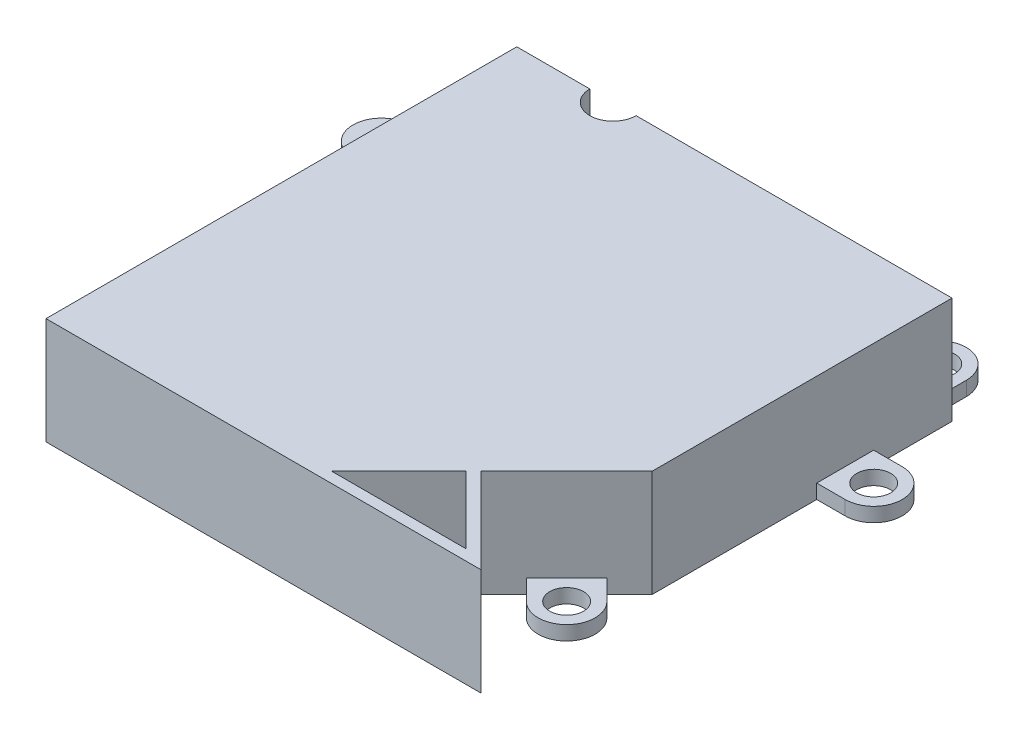
SolidWorks part; units mm, degrees
ref_plane "Front Plane" through (0, 0, 0) normal (0, 0, 1) x (1, 0, 0)
ref_plane "Top Plane" through (0, 0, 0) normal (0, 1, 0) x (1, 0, 0)
ref_plane "Right Plane" through (0, 0, 0) normal (1, 0, 0) x (0, 0, -1)
sketch "Sketch2" plane through (0, 0, 0) normal (0, 1, 0) x (1, 0, 0)
  line L0 (0, 0) -> (0, 66.1126)
  line L1 (0, 66.1126) -> (64.116, 66.1126)
  line L2 (64.116, 66.1126) -> (64.116, 23.9916)
  line L3 (64.116, 23.9916) -> (40.1244, 0)
  line L4 (40.1244, 0) -> (0, 0)
  line L5 (52.1202, 11.9958) -> (64.116, 0)
  line L6 (64.116, 0) -> (40.1244, 0)
  line L7 (52.1202, 11.9958) -> (51.0595, 10.9351)
  line L8 (51.0595, 10.9351) -> (60.4947, 1.5)
  line L9 (60.4947, 1.5) -> (41.6244, 1.5)
  dimension "D1" = 64.116
  dimension "D2" = 42.121
  dimension "D3" = 66.1126
  dimension "D4" = 135
  dimension "D5" = 40.1244
  dimension "D6" = 1.5
  dimension "D7" = 1.5
extrude "Boss-Extrude2" add sketch "Sketch2" along normal blind 15 contours L4 L3 L2 L1 L0 | L8 L9 L3 L6 L5
sketch "Sketch3" plane through (0, 0, 0) normal (0, -1, 0) x (1, 0, 0)
  line L0 (64.116, -66.1126) -> (62.616, -66.1126)
  line L1 (0, -66.1126) -> (64.116, -66.1126) construction
  line L2 (62.616, -66.1126) -> (62.616, -24.6129)
  line L3 (62.616, -24.6129) -> (39.5031, -1.5)
  line L4 (39.5031, -1.5) -> (1.5, -1.5)
  line L5 (1.5, -1.5) -> (1.5, -64.6126)
  line L6 (1.5, -64.6126) -> (62.616, -64.6126)
  line L7 (0, 0) -> (0, -66.1126) construction
  line L8 (64.116, 0) -> (0, 0) construction
  line L9 (64.116, -23.9916) -> (52.1202, -11.9958) construction
  line L10 (64.116, -66.1126) -> (64.116, -23.9916) construction
  dimension "D1" = 1.5
  dimension "D2" = 1.5
  dimension "D3" = 1.5
  dimension "D4" = 1.5
  dimension "D5" = 1.5
extrude "Cut-Extrude1" cut sketch "Sketch3" against normal blind 13.5 contours L5 L6 L2 L3 L4
sketch "Sketch4" plane through (0, 0, 0) normal (0, -1, 0) x (1, 0, 0)
  line L0 (62.616, -64.6126) -> (41.616, -64.6126)
  line L1 (1.5, -64.6126) -> (62.616, -64.6126) construction
  line L2 (41.616, -64.6126) -> (19.616, -64.6126)
  line L3 (41.616, -64.6126) -> (41.616, -66.1126)
  line L4 (0, -66.1126) -> (64.116, -66.1126) construction
  line L5 (41.616, -66.1126) -> (19.616, -66.1126)
  line L6 (19.616, -66.1126) -> (19.616, -64.6126)
  line M3 (62.616, -64.6126) -> (1.5, -64.6126)
  line M13 (0, -66.1126) -> (64.116, -66.1126)
  dimension "D1" = 21
  dimension "D2" = 22
extrude "Cut-Extrude2" cut sketch "Sketch4" against normal blind 7.5 contours L6 L3 M13 M3
sketch "Sketch5" plane through (0, 0, 0) normal (0, -1, 0) x (1, 0, 0)
  line L0 (64.116, -66.1126) -> (56.8197, -66.1126)
  line L2 (41.616, -66.1126) -> (64.116, -66.1126) construction
  line L3 (56.8197, -66.1126) -> (56.8197, -64.6126)
  line L4 (41.616, -64.6126) -> (62.616, -64.6126) construction
  line L5 (56.8197, -66.1126) -> (56.8197, -65.3626)
  line L6 (56.8197, -65.3626) -> (64.116, -65.3626)
  line L7 (64.116, -66.1126) -> (64.116, -23.9916) construction
  line L8 (56.8197, -66.1126) -> (56.8197, -66.0126)
  dimension "D1" = 0.1
sketch "Sketch6" plane through (0, 15, 0) normal (0, 1, 0) x (1, 0, 0)
  line L0 (64.116, 66.1126) -> (64.116, 65.3626)
  line L1 (64.116, 66.1126) -> (64.116, 23.9916) construction
  dimension "D1" = 0.75
ref_plane "Plane1" through (0, 0, -65.3626) normal (0, 0, 1) x (1, 0, 0)
sketch "Sketch16" plane through (0, 0, -66.1126) normal (0, 0, -1) x (-1, 0, 0)
  line L0 (-19.616, 0) -> (-9.616, 0)
  line L1 (0, 0) -> (-19.616, 0) construction
  line L2 (-9.616, 0) -> (-9.616, 9.5)
  line L3 (-9.616, 9.5) -> (-54.116, 9.5)
  line L4 (-54.116, 9.5) -> (-54.116, 0)
  line L5 (-41.616, 0) -> (-64.116, 0) construction
  line L6 (-54.116, 0) -> (-41.616, 0)
  line L7 (-41.616, 0) -> (-41.616, 7.5)
  line L8 (-41.616, 7.5) -> (-19.616, 7.5)
  line L9 (-19.616, 7.5) -> (-19.616, 0)
  dimension "D1" = 10
  dimension "D2" = 2
  dimension "D3" = 12.5
extrude "Cut-Extrude3" cut sketch "Sketch16" against normal blind 1.5
sketch "Sketch17" plane through (0, 0, 0) normal (-1, 0, 0) x (0, 0, 1)
  line L0 (-18.9306, 15) -> (0, 33.9306)
  line L1 (0, 15) -> (-66.1126, 15) construction
  line L2 (0, 33.9306) -> (0, 15)
sketch "Sketch18" plane through (0, 15, 0) normal (0, 1, 0) x (1, 0, 0)
  line L0 (0, 66.1126) -> (16.5, 66.1126)
  line L1 (0, 66.1126) -> (64.116, 66.1126) construction
  circle A0 centre (16.5, 66.1126) radius 3.25
  line M17 (64.116, 66.1126) -> (0, 66.1126)
  dimension "D2" = 6.5
  dimension "D1" = 16.5
extrude "Cut-Extrude4" cut sketch "Sketch18" against normal blind 10 contours A0 M17
sketch "Sketch21" plane through (0, 0, 0) normal (0, -1, 0) x (1, 0, 0)
  line L0 (1.5, -1.5) -> (4.5, -1.5)
  line L1 (39.5031, -1.5) -> (1.5, -1.5) construction
  line L2 (4.5, -1.5) -> (3, -1.5)
  line L3 (-10.0243, 1.3113) -> (-11.0852, 1.3113)
  line L4 (3, -1.5) -> (3, -64.6126)
  line L5 (41.1512, 35.7942) -> (40.7002, 35.8734)
  line L6 (1.5, -64.6126) -> (9.616, -64.6126) construction
  line L7 (3, -64.6126) -> (4.5, -64.6126)
  line L8 (1.5, -64.6126) -> (13.6169, -64.6126) construction
  line L9 (4.5, -64.6126) -> (4.5, -1.5)
extrude "Boss-Extrude6" add sketch "Sketch21" against normal up to surface (13.5 mm away) up to face at (28.6764, 13.5, -40.6162)
sketch "Sketch24" plane through (0, 0, 0) normal (0, -1, 0) x (1, 0, 0)
  line L0 (3, -1.5) -> (3, 0)
  line L1 (64.116, 0) -> (0, 0) construction
  line L2 (3, 0) -> (0, 0)
  line L3 (0, 0) -> (0, -66.1126)
  line L4 (0, -66.1126) -> (3, -66.1126)
  line L5 (0, -66.1126) -> (9.616, -66.1126) construction
  line L6 (3, -66.1126) -> (3, -1.5)
extrude "Cut-Extrude7" cut sketch "Sketch24" against normal through all
sketch "Sketch25" plane through (0, 0, 0) normal (0, -1, 0) x (1, 0, 0)
  line L0 (64.116, -66.1126) -> (58.116, -66.1126)
  line L1 (58.116, -66.1126) -> (54.116, -66.1126)
  line L2 (58.116, -66.1126) -> (58.116, -70.1126)
  line L3 (54.116, -70.1126) -> (54.116, -66.1126)
  line L4 (62.116, -70.1126) -> (62.116, -66.1126)
  line L5 (62.116, -66.1126) -> (58.116, -66.1126)
  arc A0 (54.116, -70.1126) -> (62.116, -70.1126) centre (58.116, -70.1126) ccw
extrude "Boss-Extrude7" add sketch "Sketch25" against normal blind 2
sketch "Sketch26" plane through (0, 0, 0) normal (0, -1, 0) x (1, 0, 0)
  line L0 (64.116, -66.1126) -> (64.116, -51.1126)
  line L1 (64.116, -66.1126) -> (64.116, -23.9916) construction
  line L2 (64.116, -51.1126) -> (68.116, -51.1126)
  line L3 (68.116, -47.1126) -> (64.116, -47.1126)
  line L4 (64.116, -47.1126) -> (64.116, -55.1126)
  line L5 (64.116, -55.1126) -> (68.116, -55.1126)
  arc A0 (68.116, -55.1126) -> (68.116, -47.1126) centre (68.116, -51.1126) ccw
extrude "Boss-Extrude8" add sketch "Sketch26" against normal blind 2
sketch "Sketch27" plane through (0, 0, 0) normal (0, -1, 0) x (1, 0, 0)
  line L0 (58.1181, -17.9937) -> (60.9465, -15.1653)
  line L1 (64.116, -23.9916) -> (52.1202, -11.9958) construction
  line L2 (58.1181, -12.3368) -> (55.2897, -15.1653)
  line L3 (55.2897, -15.1653) -> (60.9465, -20.8221)
  line L4 (60.9465, -20.8221) -> (63.775, -17.9937)
  arc A0 (63.775, -17.9937) -> (58.1181, -12.3368) centre (60.9465, -15.1653) ccw
extrude "Boss-Extrude9" add sketch "Sketch27" against normal blind 2
sketch "Sketch28" plane through (0, 0, 0) normal (0, -1, 0) x (1, 0, 0)
  line L0 (3, -66.1126) -> (3, -51.1126)
  line L1 (3, 0) -> (3, -66.1126) construction
  line L2 (3, -51.1126) -> (-1, -51.1126)
  line L3 (-1, -47.1126) -> (3, -47.1126)
  line L4 (3, -47.1126) -> (3, -55.1126)
  line L5 (3, -55.1126) -> (-1, -55.1126)
  arc A0 (-1, -55.1126) -> (-1, -47.1126) centre (-1, -51.1126) cw
extrude "Boss-Extrude10" add sketch "Sketch28" against normal blind 9
sketch "Sketch29" plane through (0, 0, 0) normal (0, -1, 0) x (1, 0, 0)
  circle A0 centre (60.9465, -15.1653) radius 2.3813
  circle A1 centre (68.116, -51.1126) radius 2.3813
  circle A2 centre (58.116, -70.1126) radius 2.3812
extrude "Cut-Extrude8" cut sketch "Sketch29" against normal through all
sketch "Sketch31" plane through (0, 0, 0) normal (0, -1, 0) x (1, 0, 0)
  circle A0 centre (-1, -51.1126) radius 2.3812
extrude "Cut-Extrude9" cut sketch "Sketch31" against normal blind 6.35
